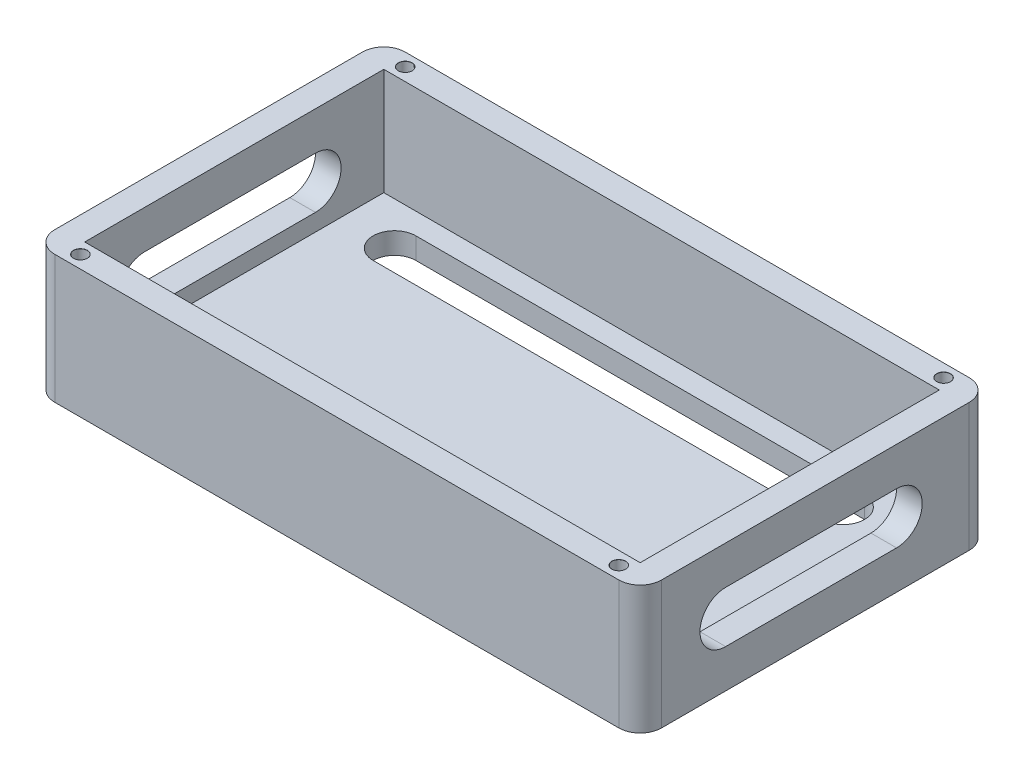
SolidWorks part; units mm, degrees
ref_plane "前视基准面" through (0, 0, 0) normal (0, 0, 1) x (1, 0, 0)
ref_plane "上视基准面" through (0, 0, 0) normal (0, 1, 0) x (1, 0, 0)
ref_plane "右视基准面" through (0, 0, 0) normal (1, 0, 0) x (0, 0, -1)
sketch "Sketch1" plane through (0, 0, 0) normal (0, 1, 0) x (1, 0, 0)
  line L1 (-71, -41) -> (71, -41)
  line L2 (-71, -41) -> (-71, 41)
  line L3 (-71, 41) -> (71, 41)
  line L4 (71, -41) -> (71, 41)
  line L5 (-71, -41) -> (71, 41) construction
  line L6 (-71, 41) -> (71, -41) construction
  point P0 (0, 0)
  dimension "D1" = 142
  dimension "D2" = 82
extrude "Boss-Extrude1" add sketch "Sketch1" along normal blind 30
sketch "Sketch3" plane through (0, 30, 0) normal (0, 1, 0) x (1, 0, 0)
  line L1 (-65, -35) -> (65, -35)
  line L2 (-65, -35) -> (-65, 35)
  line L3 (-65, 35) -> (65, 35)
  line L4 (65, -35) -> (65, 35)
  line L5 (-65, -35) -> (65, 35) construction
  line L6 (-65, 35) -> (65, -35) construction
  point P0 (0, 0)
  dimension "D1" = 130
  dimension "D2" = 70
extrude "Cut-Extrude1" cut sketch "Sketch3" against normal blind 25
fillet "Fillet1" radius 5 4 edges at (-71, 15, -41) (71, 15, -41) (71, 15, 41) (-71, 15, 41)
hole_wizard "M3 Clearance Hole1" positions "Sketch4" profile "Sketch5" hole size "M3" standard "GB" end condition through all
sketch "Sketch4" plane through (0, 30, 0) normal (0, 1, 0) x (1, 0, 0)
  line L0 (-66, -41) -> (66, -41) construction
  line L1 (71, -36) -> (71, 36) construction
  line L2 (66, 41) -> (-66, 41) construction
  line L3 (-71, 36) -> (-71, -36) construction
  point P0 (63, -38)
  point P2 (63, 38)
  point P4 (-63, 38)
  point P6 (-63, -38)
  dimension "D1" = 3
  dimension "D2" = 8
  dimension "D3" = 8
  dimension "D4" = 3
  dimension "D5" = 8
  dimension "D6" = 3
  dimension "D7" = 8
  dimension "D8" = 3
sketch "Sketch5" plane through (63, 30, 38) normal (1, 0, 0) x (0, 0, 1)
  line L0 (0, 0) -> (0, 30)
  line L1 (0, 30) -> (1.6, 30)
  line L2 (1.6, 30) -> (1.6, 0.025)
  line L3 (1.6, 0.025) -> (1.625, 0)
  line L5 (1.625, 0) -> (0, 0)
  line L6 (-1.6, 0.025) -> (-1.625, 0) construction
  line L11 (0, -6.35) -> (0, 107.95) construction
  dimension "Thru Hole Dia." = 3.2
  dimension "Thru Hole Depth" = 30
  dimension "Near C'Sink Dia." = 3.25
  dimension "Near C'Sink Angle" = 90
sketch "Sketch6" plane through (0, 5, 0) normal (0, 1, 0) x (1, 0, 0)
  line L0 (52.5, -25) -> (-52.5, -25) construction
  line L1 (52.5, -30) -> (-52.5, -30)
  line L2 (52.5, -20) -> (-52.5, -20)
  line L3 (52.5, 25) -> (-52.5, 25) construction
  line L4 (52.5, 20) -> (-52.5, 20)
  line L5 (52.5, 30) -> (-52.5, 30)
  line L6 (-65, -35) -> (65, -35) construction
  line L7 (65, 35) -> (-65, 35) construction
  line L8 (-65, 35) -> (-65, -35) construction
  line L9 (65, -35) -> (65, 35) construction
  arc A0 (52.5, -30) -> (52.5, -20) centre (52.5, -25) ccw
  arc A1 (-52.5, -20) -> (-52.5, -30) centre (-52.5, -25) ccw
  arc A2 (52.5, 20) -> (52.5, 30) centre (52.5, 25) ccw
  arc A3 (-52.5, 30) -> (-52.5, 20) centre (-52.5, 25) ccw
  point P2 (0, -25)
  point P7 (0, 25)
  dimension "D1" = 10
  dimension "D2" = 10
  dimension "D3" = 5
  dimension "D4" = 5
  dimension "D5" = 12.5
  dimension "D6" = 105
  dimension "D7" = 105
  dimension "D8" = 12.5
extrude "Cut-Extrude2" cut sketch "Sketch6" against normal up to next contours L2 A1 L1 A0 | L5 A3 L4 A2
sketch "Sketch7" plane through (71, 0, 0) normal (1, 0, 0) x (0, 0, -1)
  line L0 (-21, 15) -> (19, 15) construction
  line L1 (-21, 21) -> (19, 21)
  line L2 (-21, 9) -> (19, 9)
  line L3 (-36, 30) -> (36, 30) construction
  line L4 (-36, 30) -> (-36, 0) construction
  arc A0 (-21, 21) -> (-21, 9) centre (-21, 15) ccw
  arc A1 (19, 9) -> (19, 21) centre (19, 15) ccw
  point P2 (-1, 15)
  dimension "D1" = 40
  dimension "D2" = 6
  dimension "D3" = 15
  dimension "D4" = 15
extrude "Cut-Extrude3" cut sketch "Sketch7" against normal through all
